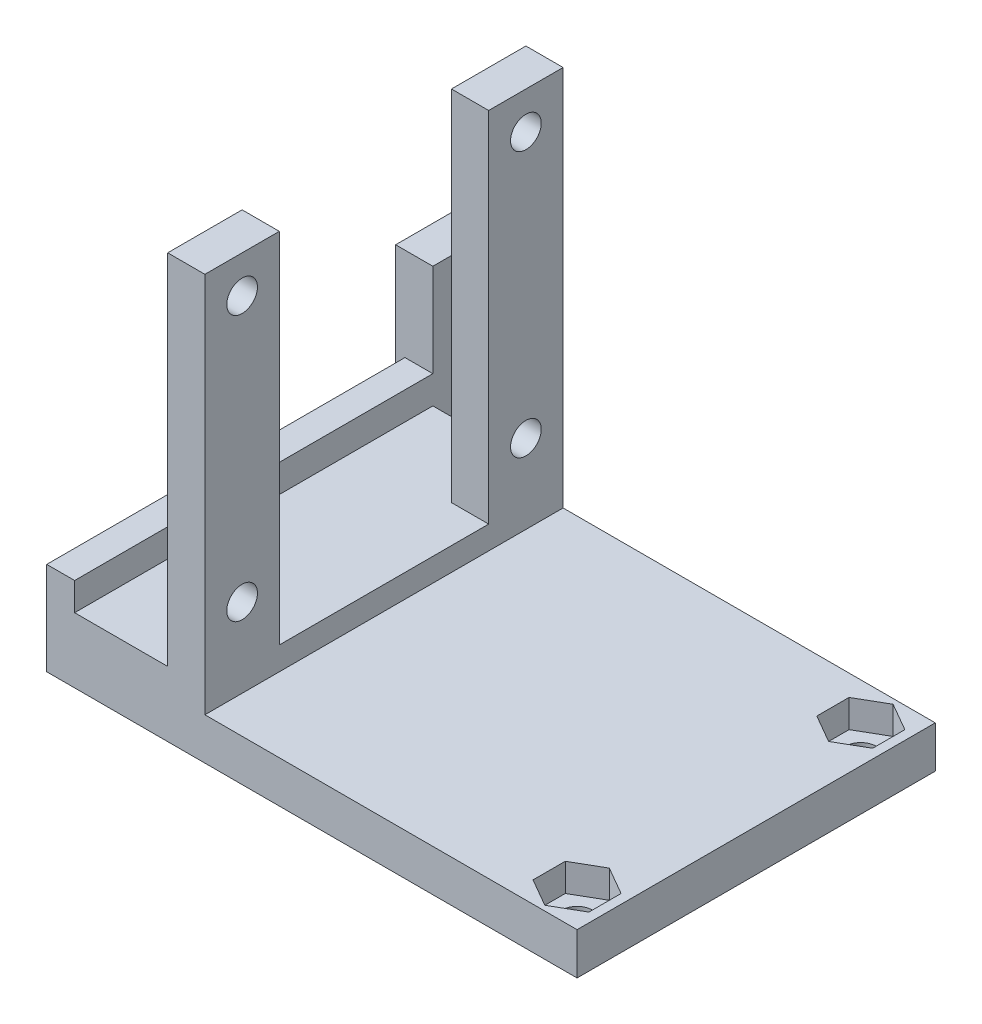
SolidWorks part; units mm, degrees
ref_plane "Front Plane" through (0, 0, 0) normal (0, 0, 1) x (1, 0, 0)
ref_plane "Top Plane" through (0, 0, 0) normal (0, 1, 0) x (1, 0, 0)
ref_plane "Right Plane" through (0, 0, 0) normal (1, 0, 0) x (0, 0, -1)
sketch "Sketch1" plane through (0, 0, 0) normal (1, 0, 0) x (0, 0, -1)
  line L1 (0, 0) -> (13, 0)
  line L2 (0, 0) -> (0, -16)
  line L3 (0, -16) -> (13, -16)
  line L4 (13, 0) -> (13, -16)
  dimension "D1" = 13
  dimension "D2" = 16
extrude "Boss-Extrude1" add sketch "Sketch1" along normal blind 4
sketch "Sketch2" plane through (4, 0, 0) normal (1, 0, 0) x (0, 0, -1)
  line L0 (13, 0) -> (0, 0) construction
  line L1 (0, -16) -> (13, -16) construction
  line L2 (13, -16) -> (13, 0) construction
  line L3 (0, 0) -> (0, -16) construction
  circle A0 centre (6.5, -4) radius 1.65
  circle A1 centre (6.5, -12) radius 1.65
  dimension "D1" = 3.3
  dimension "D2" = 3.3
  dimension "D3" = 4
  dimension "D4" = 4
  dimension "D5" = 6.5
  dimension "D6" = 6.5
extrude "Cut-Extrude1" cut sketch "Sketch2" against normal blind 10
sketch "Sketch3" plane through (0, -16, 0) normal (0, -1, 0) x (1, 0, 0)
  line L1 (4, 0) -> (0, 0)
  line L2 (4, 0) -> (4, -13)
  line L3 (4, -13) -> (0, -13)
  line L4 (0, 0) -> (0, -13)
extrude "Boss-Extrude2" add sketch "Sketch3" along normal blind 4
sketch "Sketch4" plane through (4, 0, 0) normal (1, 0, 0) x (0, 0, -1)
  line L0 (13, -20) -> (13, 0) construction
  line L1 (0, -20) -> (13, -20)
  line L2 (0, -20) -> (0, -16)
  line L3 (0, -16) -> (13, -16)
  line L4 (13, -20) -> (13, -16)
  dimension "D1" = 4
extrude "Boss-Extrude3" add sketch "Sketch4" along normal blind 60
sketch "Sketch6" plane through (0, -16, 0) normal (0, 1, 0) x (1, 0, 0)
  line L0 (64, 0) -> (4, 0) construction
  line L1 (64, 13) -> (60, 13)
  line L2 (64, 13) -> (64, -21)
  line L3 (64, -21) -> (60, -21)
  line L4 (60, 13) -> (60, -21)
  line L7 (64, 13) -> (60, 13)
  line L8 (64, 13) -> (64, 34)
  line L9 (64, 34) -> (60, 34)
  line L10 (60, 13) -> (60, 34)
  line M2 (4, 0) -> (64, 0)
  line M3 (64, 0) -> (64, 13)
  line M4 (64, 13) -> (4, 13)
  dimension "D1" = 4
  dimension "D2" = 21
  dimension "D3" = 21
extrude "Boss-Extrude4" add sketch "Sketch6" along normal blind 28 contours L4 L3 L2 M2 | L10 L8 L9 M4 | L4 M4 M2 M3
sketch "Sketch12" plane through (0, 0, -34) normal (0, 0, -1) x (-1, 0, 0)
  line L1 (-60, -16) -> (-64, -16)
  line L2 (-60, -16) -> (-60, 12)
  line L3 (-60, 12) -> (-64, 12)
  line L4 (-64, -16) -> (-64, 12)
extrude "Boss-Extrude8" add sketch "Sketch12" along normal blind 1.65
sketch "Sketch13" plane through (0, 0, 21) normal (0, 0, 1) x (1, 0, 0)
  line L1 (60, 12) -> (64, 12)
  line L2 (60, 12) -> (60, -16)
  line L3 (60, -16) -> (64, -16)
  line L4 (64, 12) -> (64, -16)
extrude "Boss-Extrude9" add sketch "Sketch13" along normal blind 1.65
sketch "Sketch14" plane through (0, 12, 0) normal (0, 1, 0) x (1, 0, 0)
  line L0 (64, 35.65) -> (64, -22.65) construction
  line L1 (64, 24.35) -> (60, 24.35)
  line L2 (64, 24.35) -> (64, -11.5284)
  line L3 (64, -11.5284) -> (60, -11.5284)
  line L4 (60, 24.35) -> (60, -11.5284)
  line L5 (60, 35.65) -> (60, -22.65) construction
  line L6 (64, -22.65) -> (60, -22.65) construction
  line L7 (60, 35.65) -> (64, 35.65) construction
  point P10 (62, -22.65)
  dimension "D1" = 11.3
  dimension "D2" = 11.3
extrude "Cut-Extrude5" cut sketch "Sketch14" against normal blind 24
sketch "Sketch15" plane through (64, 0, 0) normal (1, 0, 0) x (0, 0, -1)
  line L0 (-11.5284, 12) -> (-22.65, 12) construction
  line L1 (35.65, 12) -> (24.35, 12) construction
  line L2 (-22.65, -16) -> (-22.65, 12) construction
  line L3 (35.65, 12) -> (35.65, -16) construction
  circle A0 centre (-17, -11.5) radius 1.65
  circle A1 centre (30, -11.5) radius 1.65
  dimension "D1" = 3.3
  dimension "D2" = 3.3
  dimension "D3" = 23.5
  dimension "D4" = 23.5
  dimension "D5" = 5.65
  dimension "D6" = 5.65
extrude "Cut-Extrude6" cut sketch "Sketch15" against normal blind 24
sketch "Sketch16" plane through (0, 12, 0) normal (0, 1, 0) x (1, 0, 0)
  line L1 (60, -22.65) -> (64, -22.65)
  line L2 (60, -22.65) -> (60, -11.5284)
  line L3 (60, -11.5284) -> (64, -11.5284)
  line L4 (64, -22.65) -> (64, -11.5284)
  line L5 (60, 24.35) -> (64, 24.35)
  line L6 (60, 24.35) -> (60, 35.65)
  line L7 (60, 35.65) -> (64, 35.65)
  line L8 (64, 24.35) -> (64, 35.65)
extrude "Boss-Extrude10" add sketch "Sketch16" along normal blind 29.15
sketch "Sketch17" plane through (64, 0, 0) normal (1, 0, 0) x (0, 0, -1)
  line L0 (-22.65, -16) -> (-22.65, 41.15) construction
  line L1 (35.65, 41.15) -> (35.65, -16) construction
  line L2 (-22.65, 41.15) -> (-11.5284, 41.15) construction
  line L3 (24.35, 41.15) -> (35.65, 41.15) construction
  circle A0 centre (-17, 35.5) radius 1.65
  circle A1 centre (30, 35.5) radius 1.65
  dimension "D1" = 3.3
  dimension "D2" = 3.3
  dimension "D4" = 5.65
  dimension "D3" = 5.65
  dimension "D5" = 5.65
  dimension "D6" = 5.65
extrude "Cut-Extrude8" cut sketch "Sketch17" against normal blind 29.15
sketch "Sketch18" plane through (64, 0, 0) normal (1, 0, 0) x (0, 0, -1)
  line L1 (-22.65, -16) -> (13, -16)
  line L2 (-22.65, -16) -> (-22.65, -20)
  line L3 (-22.65, -20) -> (13, -20)
  line L4 (13, -16) -> (13, -20)
  line L5 (0, -20) -> (35.65, -20)
  line L6 (0, -20) -> (0, -16)
  line L7 (0, -16) -> (35.65, -16)
  line L8 (35.65, -20) -> (35.65, -16)
  line M9 (-22.65, -16) -> (0, -16)
  line M10 (0, -16) -> (0, -20)
  line M11 (0, -20) -> (13, -20)
  line M12 (13, -20) -> (13, -16)
  line M13 (13, -16) -> (35.65, -16)
extrude "Boss-Extrude11" add sketch "Sketch18" against normal blind 4 contours L2 L3 M10 M9 | L5 L8 M13 M12 | L1 M10 M11 M12
sketch "Sketch19" plane through (0, 0, -13) normal (0, 0, -1) x (-1, 0, 0)
  line L1 (0, -20) -> (-4, -20)
  line L2 (0, -20) -> (0, 0)
  line L3 (0, 0) -> (-4, 0)
  line L4 (-4, -20) -> (-4, 0)
extrude "Boss-Extrude12" add sketch "Sketch19" along normal blind 40
sketch "Sketch20" plane through (0, 0, 0) normal (-1, 0, 0) x (0, 0, 1)
  line L0 (-53, 0) -> (0, 0) construction
  line L1 (-53, -20) -> (-53, 0) construction
  circle A0 centre (-46.5, -4) radius 1.65
  circle A1 centre (-46.5, -12) radius 1.65
  dimension "D1" = 3.3
  dimension "D2" = 3.3
  dimension "D3" = 4
  dimension "D4" = 8
  dimension "D5" = 6.5
  dimension "D6" = 6.5
extrude "Cut-Extrude9" cut sketch "Sketch20" against normal blind 40
sketch "Sketch21" plane through (0, -16, 0) normal (0, 1, 0) x (1, 0, 0)
  line L0 (4, 53) -> (4, 13) construction
  line L1 (28, 21.75) -> (24, 21.75)
  line L2 (28, 21.75) -> (28, -8.75)
  line L3 (28, -8.75) -> (24, -8.75)
  line L4 (24, 21.75) -> (24, -8.75)
  line L5 (60, 13) -> (4, 13) construction
  line L6 (60, 0) -> (4, 0) construction
  dimension "D1" = 20
  dimension "D2" = 4
  dimension "D3" = 8.75
  dimension "D4" = 8.75
extrude "Boss-Extrude13" add sketch "Sketch21" along normal blind 38.5
sketch "Sketch23" plane through (0, 22.5, 0) normal (0, 1, 0) x (1, 0, 0)
  line L1 (24, 21.75) -> (28, 21.75)
  line L2 (24, 21.75) -> (24, 25.75)
  line L3 (24, 25.75) -> (28, 25.75)
  line L4 (28, 21.75) -> (28, 25.75)
  line L6 (24, 21.75) -> (24, -8.75) construction
  line L7 (28, -8.75) -> (28, 21.75) construction
  line L8 (24, -8.75) -> (28, -8.75)
  line L9 (24, -8.75) -> (24, -12.75)
  line L10 (24, -12.75) -> (28, -12.75)
  line L11 (28, -8.75) -> (28, -12.75)
  dimension "D1" = 4
  dimension "D2" = 4
  dimension "D3" = 4
  dimension "D4" = 0
extrude "Boss-Extrude14" add sketch "Sketch23" against normal blind 38.5
sketch "Sketch24" plane through (0, 22.5, 0) normal (0, 1, 0) x (1, 0, 0)
  line L1 (28, 25.75) -> (24, 25.75)
  line L2 (28, 25.75) -> (28, -12.75)
  line L3 (28, -12.75) -> (24, -12.75)
  line L4 (24, 25.75) -> (24, -12.75)
extrude "Boss-Extrude15" add sketch "Sketch24" along normal blind 3
sketch "Sketch25" plane through (28, 0, 0) normal (1, 0, 0) x (0, 0, -1)
  line L0 (25.75, -16) -> (25.75, 25.5) construction
  line L1 (25.75, -13) -> (-12.75, -13)
  line L2 (25.75, -13) -> (25.75, -20)
  line L3 (25.75, -20) -> (-12.75, -20)
  line L4 (-12.75, -13) -> (-12.75, -20)
  line L5 (13, -16) -> (25.75, -16) construction
  line L6 (-12.75, -16) -> (0, -16) construction
  line L7 (-12.75, -16) -> (-12.75, 25.5) construction
  dimension "D1" = 3
  dimension "D2" = 4
  dimension "D3" = 0
sketch "Sketch27" plane through (0, -20, 0) normal (0, -1, 0) x (1, 0, 0)
  line L1 (64, 22.65) -> (60, 22.65)
  line L2 (64, 22.65) -> (64, -35.65)
  line L3 (64, -35.65) -> (60, -35.65)
  line L4 (60, 22.65) -> (60, -35.65)
extrude "Cut-Extrude10" cut sketch "Sketch27" against normal blind 100
sketch "Sketch29" plane through (28, 0, 0) normal (1, 0, 0) x (0, 0, -1)
  line L2 (-12.75, -13) -> (25.75, -13)
  line L3 (-12.75, -13) -> (-12.75, -20)
  line L4 (-12.75, -20) -> (25.75, -20)
  line L5 (25.75, -13) -> (25.75, -20)
extrude "Boss-Extrude16" add sketch "Sketch29" along normal blind 40 and the other way blind 28
sketch "Sketch30" plane through (24, 0, 0) normal (-1, 0, 0) x (0, 0, 1)
  line L0 (12.75, -13) -> (12.75, 25.5) construction
  line L1 (-25.75, 25.5) -> (12.75, 25.5) construction
  line L2 (-25.75, -13) -> (12.75, -13) construction
  line L3 (-25.75, -13) -> (-25.75, 25.5) construction
  circle A0 centre (8.75, 21.5) radius 1.65
  circle A1 centre (8.75, -9) radius 1.65
  circle A2 centre (-21.75, 21.5) radius 1.65
  circle A3 centre (-21.75, -9) radius 1.65
  dimension "D1" = 3.3
  dimension "D4" = 3.3
  dimension "D7" = 3.3
  dimension "D12" = 3.3
  dimension "D2" = 4
  dimension "D3" = 4
  dimension "D5" = 4
  dimension "D6" = 4
  dimension "D8" = 4
  dimension "D9" = 4
  dimension "D10" = 4
  dimension "D11" = 4
extrude "Cut-Extrude11" cut sketch "Sketch30" against normal blind 40
sketch "Sketch31" plane through (0, 25.5, 0) normal (0, 1, 0) x (1, 0, 0)
  line L0 (28, -12.75) -> (28, 25.75) construction
  line L1 (28, 17.75) -> (24, 17.75)
  line L2 (28, 17.75) -> (28, -4.75)
  line L3 (28, -4.75) -> (24, -4.75)
  line L4 (24, 17.75) -> (24, -4.75)
  line L5 (24, 25.75) -> (24, -12.75) construction
  line L6 (24, -12.75) -> (28, -12.75) construction
  dimension "D1" = 8
  dimension "D2" = 8
extrude "Cut-Extrude12" cut sketch "Sketch31" against normal blind 38.5
sketch "Sketch32" plane through (68, 0, 0) normal (1, 0, 0) x (0, 0, -1)
  line L0 (25.75, -20) -> (25.75, -13) construction
  line L1 (-12.75, -13) -> (25.75, -13)
  line L2 (-12.75, -13) -> (-12.75, -15.5)
  line L3 (-12.75, -15.5) -> (25.75, -15.5)
  line L4 (25.75, -13) -> (25.75, -15.5)
  dimension "D1" = 2.5
extrude "Cut-Extrude13" cut sketch "Sketch32" against normal blind 40
sketch "Sketch33" plane through (0, 25.5, 0) normal (0, 1, 0) x (1, 0, 0)
  line L1 (24, -12.75) -> (28, -12.75)
  line L2 (24, -12.75) -> (24, -4.75)
  line L3 (24, -4.75) -> (28, -4.75)
  line L4 (28, -12.75) -> (28, -4.75)
  line L5 (24, 17.75) -> (28, 17.75)
  line L6 (24, 17.75) -> (24, 25.75)
  line L7 (24, 25.75) -> (28, 25.75)
  line L8 (28, 17.75) -> (28, 25.75)
extrude "Boss-Extrude17" add sketch "Sketch33" against normal blind 8
sketch "Sketch34" plane through (28, 0, 0) normal (1, 0, 0) x (0, 0, -1)
  line L0 (-12.75, 25.5) -> (-4.75, 25.5) construction
  line L1 (-12.75, -15.5) -> (-12.75, 25.5) construction
  line L2 (25.75, -15.5) -> (25.75, 25.5) construction
  line L3 (17.75, 25.5) -> (25.75, 25.5) construction
  circle A0 centre (-8.75, 21.5) radius 1.65
  circle A1 centre (21.75, 21.5) radius 1.65
  dimension "D1" = 3.3
  dimension "D2" = 3.3
  dimension "D3" = 4
  dimension "D4" = 4
  dimension "D5" = 4
  dimension "D6" = 4
extrude "Cut-Extrude14" cut sketch "Sketch34" against normal blind 8
sketch "Sketch35" plane through (0, -13, 0) normal (0, 1, 0) x (1, 0, 0)
  line L0 (0, -12.75) -> (24, -12.75) construction
  line L1 (10, -12.75) -> (14, -12.75)
  line L2 (10, -12.75) -> (10, 30.75)
  line L3 (10, 30.75) -> (14, 30.75)
  line L4 (14, -12.75) -> (14, 30.75)
  line L5 (24, 25.75) -> (24, 17.75) construction
  line L6 (4, 25.75) -> (24, 25.75) construction
  dimension "D1" = 10
  dimension "D2" = 4
  dimension "D3" = 5
extrude "Boss-Extrude18" add sketch "Sketch35" along normal blind 13
sketch "Sketch36" plane through (0, -20, 0) normal (0, -1, 0) x (1, 0, 0)
  line L1 (0, 12.75) -> (68, 12.75) construction
  line L2 (0, 12.75) -> (10, 12.75)
  line L3 (0, 12.75) -> (0, -67.25)
  line L4 (0, -67.25) -> (10, -67.25)
  line L5 (10, 12.75) -> (10, -67.25)
  line L6 (4, -53) -> (4, -25.75) construction
  dimension "D1" = 10
  dimension "D2" = 80
  dimension "D3" = 4
extrude "Cut-Extrude15" cut sketch "Sketch36" against normal up to vertex
sketch "Sketch37" plane through (10, 0, 0) normal (-1, 0, 0) x (0, 0, 1)
  line L1 (-30.75, -13) -> (-25.75, -13)
  line L2 (-30.75, -13) -> (-30.75, -20)
  line L3 (-30.75, -20) -> (-25.75, -20)
  line L4 (-25.75, -13) -> (-25.75, -20)
extrude "Boss-Extrude19" add sketch "Sketch37" against normal blind 4
sketch "Sketch41" plane through (14, 0, 0) normal (1, 0, 0) x (0, 0, -1)
  line L1 (25.75, -20) -> (38.75, -20)
  line L2 (25.75, -20) -> (25.75, 0)
  line L3 (25.75, 0) -> (38.75, 0)
  line L4 (38.75, -20) -> (38.75, 0)
  dimension "D1" = 13
  dimension "D2" = 20
extrude "Boss-Extrude20" add sketch "Sketch41" against normal blind 4
sketch "Sketch42" plane through (10, 0, 0) normal (-1, 0, 0) x (0, 0, 1)
  line L0 (-38.75, 0) -> (12.75, 0) construction
  line L1 (-38.75, -20) -> (-38.75, 0) construction
  circle A0 centre (-32.25, -4) radius 1.65
  circle A1 centre (-32.25, -12) radius 1.65
  dimension "D1" = 3.3
  dimension "D2" = 3.3
  dimension "D3" = 4
  dimension "D4" = 6.5
  dimension "D5" = 8
  dimension "D6" = 6.5
extrude "Cut-Extrude18" cut sketch "Sketch42" against normal blind 4
sketch "Sketch43" plane through (0, 0, 0) normal (0, 1, 0) x (1, 0, 0)
  line L0 (10, 38.75) -> (10, -12.75) construction
  line L1 (14, -12.75) -> (10, -12.75)
  line L2 (14, -12.75) -> (14, 25.75)
  line L3 (14, 25.75) -> (10, 25.75)
  line L4 (10, -12.75) -> (10, 25.75)
  line L5 (10, 38.75) -> (14, 38.75) construction
  dimension "D1" = 13
extrude "Cut-Extrude19" cut sketch "Sketch43" against normal blind 10
sketch "Sketch44" plane through (28, 0, 0) normal (1, 0, 0) x (0, 0, -1)
  line L0 (-4.75, -13) -> (-4.75, 25.5) construction
  line L1 (-12.75, -15.5) -> (-4.75, -15.5)
  line L2 (-12.75, -15.5) -> (-12.75, -6.5)
  line L3 (-12.75, -6.5) -> (-4.75, -6.5)
  line L4 (-4.75, -15.5) -> (-4.75, -6.5)
  line L5 (17.75, -13) -> (17.75, 25.5) construction
  line L6 (25.75, -15.5) -> (17.75, -15.5)
  line L7 (25.75, -15.5) -> (25.75, -6.5)
  line L8 (25.75, -6.5) -> (17.75, -6.5)
  line L9 (17.75, -15.5) -> (17.75, -6.5)
  dimension "D1" = 9
  dimension "D2" = 9
extrude "Boss-Extrude21" add sketch "Sketch44" against normal blind 4
sketch "Sketch45" plane through (24, 0, 0) normal (-1, 0, 0) x (0, 0, 1)
  line L0 (4.75, -13) -> (12.75, -13) construction
  line L1 (-25.75, -13) -> (-17.75, -13) construction
  line L2 (-25.75, -13) -> (-25.75, 25.5) construction
  line L3 (12.75, -13) -> (12.75, 25.5) construction
  circle A0 centre (-21.75, -7) radius 1.65
  circle A1 centre (8.75, -7) radius 1.65
  dimension "D1" = 3.3
  dimension "D2" = 3.3
  dimension "D3" = 6
  dimension "D4" = 6
  dimension "D5" = 4
  dimension "D6" = 4
extrude "Cut-Extrude20" cut sketch "Sketch45" against normal blind 4
sketch "Sketch46" plane through (0, -15.5, 0) normal (0, 1, 0) x (1, 0, 0)
  line L0 (68, -12.75) -> (68, 25.75) construction
  line L1 (64, 18.2859) -> (67, 20.0179)
  line L2 (67, 20.0179) -> (67, 23.4821)
  line L3 (67, 23.4821) -> (64, 25.2141)
  line L4 (64, 25.2141) -> (61, 23.4821)
  line L5 (61, 23.4821) -> (61, 20.0179)
  line L6 (61, 20.0179) -> (64, 18.2859)
  line L7 (64, -12.2141) -> (67, -10.4821)
  line L8 (67, -10.4821) -> (67, -7.0179)
  line L9 (67, -7.0179) -> (64, -5.2859)
  line L10 (64, -5.2859) -> (61, -7.0179)
  line L11 (61, -7.0179) -> (61, -10.4821)
  line L12 (61, -10.4821) -> (64, -12.2141)
  line L13 (28, 25.75) -> (68, 25.75) construction
  line L14 (28, -12.75) -> (68, -12.75) construction
  circle A0 centre (64, 21.75) radius 3 construction
  circle A1 centre (64, -8.75) radius 3 construction
  dimension "D3" = 6
  dimension "D7" = 6
  dimension "D1" = 4
  dimension "D2" = 4
  dimension "D4" = 1
  dimension "D5" = 4
  dimension "D6" = 4
  dimension "D8" = 1
extrude "Cut-Extrude21" cut sketch "Sketch46" against normal blind 3
sketch "Sketch49" plane through (0, -15.5, 0) normal (0, 1, 0) x (1, 0, 0)
  line L0 (68, -12.75) -> (68, 25.75) construction
  line L1 (28, 25.75) -> (68, 25.75) construction
  line L2 (28, -12.75) -> (68, -12.75) construction
  circle A0 centre (64, 21.75) radius 1.65
  circle A1 centre (64, -8.75) radius 1.65
  point P8 (58.4858, 40.9665)
  dimension "D1" = 3.3
  dimension "D2" = 3.3
  dimension "D3" = 4
  dimension "D4" = 4
  dimension "D5" = 4
  dimension "D6" = 4
extrude "Cut-Extrude22" cut sketch "Sketch49" against normal blind 5
ref_plane "Plane1" through (10, -10, -25.75) normal (0, 0, 1) x (1, 0, 0)
sketch "Sketch54" plane through (0, -10, 0) normal (0, 1, 0) x (1, 0, 0)
  line L0 (10, -12.75) -> (14, -12.75) construction
  line L1 (10, 25.75) -> (11, 25.75)
  line L2 (10, 25.75) -> (10, -12.75)
  line L3 (10, -12.75) -> (11, -12.75)
  line L4 (11, 25.75) -> (11, -12.75)
  dimension "D1" = 1
  dimension "D2" = 0
extrude "Cut-Extrude24" cut sketch "Sketch54" against normal blind 50
